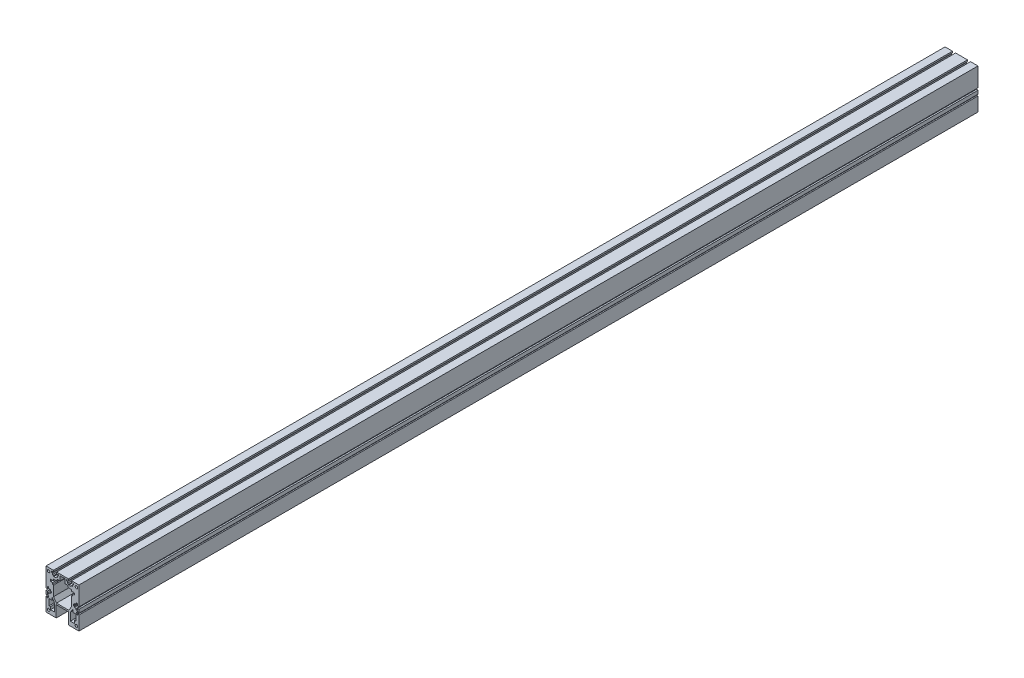
SolidWorks part; units mm, degrees
ref_plane "前视基准面" through (0, 0, 0) normal (0, 0, 1) x (1, 0, 0)
ref_plane "上视基准面" through (0, 0, 0) normal (0, 1, 0) x (1, 0, 0)
ref_plane "右视基准面" through (0, 0, 0) normal (1, 0, 0) x (0, 0, -1)
sketch "草图2" plane through (0, 0, 0) normal (0, 0, 1) x (1, 0, 0)
  line L0 (-18.1, 40) -> (-18.1, 37)
  line L1 (-33, 40) -> (-18.1, 40)
  line L2 (-33, 40) -> (-33, 2.0496)
  line L3 (-33, -40) -> (33, -40)
  line L4 (33, 40) -> (33, 2.0496)
  line L5 (-33, 40) -> (33, -40) construction
  line L6 (-33, -40) -> (33, 40) construction
  line L7 (-27.8, 33.5) -> (27.8, 33.5) construction
  line L8 (-27.8, 33.5) -> (-27.8, -33.5) construction
  line L9 (-27.8, -33.5) -> (27.8, -33.5) construction
  line L10 (27.8, 33.5) -> (27.8, -33.5) construction
  line L11 (-27.8, 33.5) -> (27.8, -33.5) construction
  line L12 (-27.8, -33.5) -> (27.8, 33.5) construction
  line L13 (-18.1, 37) -> (-22.1, 37)
  line L14 (-22.1, 37) -> (-22.1, 34.5)
  line L15 (-22.1, 34.5) -> (-20.1, 34.5)
  line L16 (-20.1, 34.5) -> (-20.1, 31)
  line L17 (-20.1, 31) -> (-17.5, 31)
  line L18 (-17.5, 31) -> (-17.5, 29.4)
  line L19 (-17.5, 29.4) -> (-12.5, 29.4)
  line L20 (-15, 29.4) -> (-15, 48.3161) construction
  line L21 (-12.5, 31) -> (-12.5, 29.4)
  line L22 (-9.9, 31) -> (-12.5, 31)
  line L23 (-9.9, 34.5) -> (-9.9, 31)
  line L24 (-7.9, 34.5) -> (-9.9, 34.5)
  line L25 (-7.9, 37) -> (-7.9, 34.5)
  line L26 (-11.9, 37) -> (-7.9, 37)
  line L27 (-11.9, 40) -> (-11.9, 37)
  line L28 (-11.9, 40) -> (11.9, 40)
  line L29 (0, 0) -> (0, 48.3161) construction
  line L30 (11.9, 40) -> (11.9, 37)
  line L31 (11.9, 37) -> (7.9, 37)
  line L32 (7.9, 37) -> (7.9, 34.5)
  line L33 (7.9, 34.5) -> (9.9, 34.5)
  line L34 (9.9, 34.5) -> (9.9, 31)
  line L35 (9.9, 31) -> (12.5, 31)
  line L36 (12.5, 31) -> (12.5, 29.4)
  line L37 (17.5, 29.4) -> (12.5, 29.4)
  line L38 (17.5, 31) -> (17.5, 29.4)
  line L39 (20.1, 31) -> (17.5, 31)
  line L40 (20.1, 34.5) -> (20.1, 31)
  line L41 (22.1, 34.5) -> (20.1, 34.5)
  line L42 (22.1, 37) -> (22.1, 34.5)
  line L43 (18.1, 37) -> (22.1, 37)
  line L44 (18.1, 40) -> (18.1, 37)
  line L45 (18.1, 40) -> (33, 40)
  line L46 (-24.0002, 21.7881) -> (-17.9322, 21.7881)
  line L47 (-17.9322, 21.7881) -> (-17.9322, 24.7125)
  line L48 (-17.9322, 24.7125) -> (-10.6389, 24.7125)
  line L49 (-10.6389, 24.7125) -> (-10.6389, 28.1692)
  line L50 (-10.6389, 28.1692) -> (-4.9, 28.1692)
  line L51 (-4.9, 28.1692) -> (-4.9, 37)
  line L52 (-4.9, 37) -> (4.9, 37)
  line L53 (-24.0002, 21.7881) -> (-24.0002, 17.5528)
  line L54 (-24.0002, 17.5528) -> (-20.1431, 17.5528)
  line L55 (-20.1431, 17.5528) -> (-20.1431, 14.1747)
  line L56 (-20.1431, 14.1747) -> (-17.9322, 14.1747)
  line L57 (-17.9322, 14.1747) -> (-17.9322, -5.7521)
  line L58 (-17.9322, -5.7521) -> (-12.0458, -14)
  line L59 (-12.0458, -14) -> (0, -14)
  line L60 (0, 0) -> (0, -54.8405) construction
  line L61 (4.9, 28.1692) -> (4.9, 37)
  line L62 (10.6389, 24.7125) -> (10.6389, 28.1692)
  line L63 (10.6389, 28.1692) -> (4.9, 28.1692)
  line L64 (17.9322, 24.7125) -> (10.6389, 24.7125)
  line L65 (17.9322, 21.7881) -> (17.9322, 24.7125)
  line L66 (24.0002, 21.7881) -> (17.9322, 21.7881)
  line L67 (24.0002, 21.7881) -> (24.0002, 17.5528)
  line L68 (27.8, -33.5) -> (-27.8, 33.5) construction
  line L69 (27.8, 33.5) -> (-27.8, -33.5) construction
  line L70 (12.0458, -14) -> (0, -14)
  line L71 (17.9322, -5.7521) -> (12.0458, -14)
  line L72 (17.9322, 14.1747) -> (17.9322, -5.7521)
  line L73 (20.1431, 14.1747) -> (17.9322, 14.1747)
  line L74 (20.1431, 17.5528) -> (20.1431, 14.1747)
  line L75 (24.0002, 17.5528) -> (20.1431, 17.5528)
  line L76 (-12.5, -40) -> (-12.5, -17)
  line L77 (-12.5, -17) -> (12.5, -17)
  line L78 (12.5, -17) -> (12.5, -40)
  line L79 (-33, -2.0496) -> (-30, -2.0496)
  line L80 (-30, -2.0496) -> (-30, -6.3482)
  line L81 (-27.8, -2.7555) -> (-26.6442, -2.7555)
  line L82 (-30, -6.3482) -> (-27.5, -6.3482)
  line L83 (-27.5, -6.3482) -> (-27.5, -3.5932)
  line L84 (-27.5, -3.5932) -> (-24, -3.5932)
  line L85 (-24, -3.5932) -> (-24, -1.3766)
  line L86 (-22.4, -1.3766) -> (-22.4, 1.3766)
  line L87 (-24, 1.3766) -> (-22.4, 1.3766)
  line L88 (-24, 3.5932) -> (-24, 1.3766)
  line L89 (-27.5, 3.5932) -> (-24, 3.5932)
  line L90 (-27.5, 6.3482) -> (-27.5, 3.5932)
  line L91 (-30, 6.3482) -> (-27.5, 6.3482)
  line L92 (-30, 2.0496) -> (-30, 6.3482)
  line L93 (-33, 2.0496) -> (-30, 2.0496)
  line L94 (24, -1.3766) -> (22.4, -1.3766)
  line L95 (33, 2.0496) -> (30, 2.0496)
  line L96 (30, 2.0496) -> (30, 6.3482)
  line L97 (30, 6.3482) -> (27.5, 6.3482)
  line L98 (27.5, 6.3482) -> (27.5, 3.5932)
  line L99 (27.5, 3.5932) -> (24, 3.5932)
  line L100 (24, 3.5932) -> (24, 1.3766)
  line L101 (24, 1.3766) -> (22.4, 1.3766)
  line L102 (22.4, -1.3766) -> (22.4, 1.3766)
  line L103 (24, -3.5932) -> (24, -1.3766)
  line L104 (27.5, -3.5932) -> (24, -3.5932)
  line L105 (27.5, -6.3482) -> (27.5, -3.5932)
  line L106 (30, -6.3482) -> (27.5, -6.3482)
  line L107 (27.8, -2.7555) -> (26.6442, -2.7555)
  line L108 (30, -2.0496) -> (30, -6.3482)
  line L109 (-20.9431, -8.11) -> (-15.8, -15.8603)
  line L110 (-15.8, -15.8603) -> (-15.8, -31.3609)
  line L111 (-15.8, -31.3609) -> (-24, -31.3609)
  line L112 (-24, -31.3609) -> (-24, -25.867)
  line L113 (-24, -25.867) -> (-26.6442, -25.867)
  line L114 (-26.6442, -25.867) -> (-26.6442, -13.4541)
  line L115 (-26.6442, -13.4541) -> (-20.9431, -13.4541)
  line L116 (-20.9431, -13.4541) -> (-20.9431, -8.11)
  line L117 (-33, -9.0684) -> (-30.7298, -9.0684)
  line L118 (-30.7298, -9.0684) -> (-30.7298, -7.473)
  line L119 (-30.7298, -7.473) -> (-29.1441, -7.473)
  line L120 (-29.1441, -7.473) -> (-29.1441, -9.0684)
  line L121 (-29.1441, -9.0684) -> (-27.8, -9.0684)
  line L122 (-27.8, -9.0684) -> (-27.8, -10.5684)
  line L123 (-36.4558, -10.5684) -> (-24.4752, -10.5684) construction
  line L124 (-27.8, -12.0684) -> (-27.8, -9.0684)
  line L125 (-29.1441, -12.0684) -> (-27.8, -12.0684)
  line L126 (-29.1441, -13.6637) -> (-29.1441, -12.0684)
  line L127 (-30.7298, -13.6637) -> (-29.1441, -13.6637)
  line L128 (-30.7298, -12.0684) -> (-30.7298, -13.6637)
  line L129 (-33, -12.0684) -> (-30.7298, -12.0684)
  line L130 (-33, -9.0684) -> (-30.7298, -9.0684)
  line L131 (-30.7298, -9.0684) -> (-30.7298, -7.473)
  line L132 (-30.7298, -7.473) -> (-29.1441, -7.473)
  line L133 (-29.1441, -7.473) -> (-29.1441, -9.0684)
  line L134 (-29.1441, -9.0684) -> (-27.8, -9.0684)
  line L135 (-27.8, -12.0684) -> (-27.8, -10.5684)
  line L136 (-29.1441, -12.0684) -> (-27.8, -12.0684)
  line L137 (-29.1441, -13.6637) -> (-29.1441, -12.0684)
  line L138 (-30.7298, -13.6637) -> (-29.1441, -13.6637)
  line L139 (-30.7298, -12.0684) -> (-30.7298, -13.6637)
  line L140 (-33, -12.0684) -> (-30.7298, -12.0684)
  line L141 (29.1441, -12.0684) -> (27.8, -12.0684)
  line L142 (29.1441, -13.6637) -> (29.1441, -12.0684)
  line L143 (24, -31.3609) -> (24, -25.867)
  line L144 (15.8, -31.3609) -> (24, -31.3609)
  line L145 (15.8, -15.8603) -> (15.8, -31.3609)
  line L146 (20.9431, -13.4541) -> (20.9431, -8.11)
  line L147 (26.6442, -13.4541) -> (20.9431, -13.4541)
  line L148 (26.6442, -25.867) -> (26.6442, -13.4541)
  line L149 (24, -25.867) -> (26.6442, -25.867)
  line L150 (20.9431, -8.11) -> (15.8, -15.8603)
  line L151 (33, -12.0684) -> (30.7298, -12.0684)
  line L152 (30.7298, -12.0684) -> (30.7298, -13.6637)
  line L153 (30.7298, -13.6637) -> (29.1441, -13.6637)
  line L154 (29.1441, -9.0684) -> (27.8, -9.0684)
  line L155 (29.1441, -7.473) -> (29.1441, -9.0684)
  line L156 (30.7298, -7.473) -> (29.1441, -7.473)
  line L157 (30.7298, -9.0684) -> (30.7298, -7.473)
  line L158 (33, -9.0684) -> (30.7298, -9.0684)
  line L159 (33, -12.0684) -> (30.7298, -12.0684)
  line L160 (30.7298, -12.0684) -> (30.7298, -13.6637)
  line L161 (30.7298, -13.6637) -> (29.1441, -13.6637)
  line L162 (27.8, -12.0684) -> (27.8, -9.0684)
  line L163 (27.8, -9.0684) -> (27.8, -10.5684)
  line L164 (29.1441, -9.0684) -> (27.8, -9.0684)
  line L165 (29.1441, -7.473) -> (29.1441, -9.0684)
  line L166 (30.7298, -7.473) -> (29.1441, -7.473)
  line L167 (30.7298, -9.0684) -> (30.7298, -7.473)
  line L168 (33, -9.0684) -> (30.7298, -9.0684)
  line L169 (33, -2.0496) -> (30, -2.0496)
  line L170 (33, 1.2445) -> (33, -9.0684)
  line L171 (33, -12.0684) -> (33, -40)
  line L172 (-22.4, 0) -> (-43.3501, 0) construction
  line L173 (-24, -1.3766) -> (-22.4, -1.3766)
  line L174 (-33, -2.0496) -> (-33, -40)
  circle A0 centre (-27.8, 33.5) radius 2.5
  circle A1 centre (27.8, 33.5) radius 2.5
  circle A2 centre (27.8, -33.5) radius 2.5
  circle A3 centre (-27.8, -33.5) radius 2.5
  point P0 (0, 0)
  point P7 (0, 0)
  point P32 (-18.1, 38.5)
  point P69 (0, 37)
  point P85 (0, -17)
  point P137 (-27.8, -9.8184)
  point P138 (-27.8, -11.3184)
  point P145 (-27.8, -9.8184)
  dimension "D5" = 5
  dimension "D6" = 5
  dimension "D7" = 5
  dimension "D8" = 5
  dimension "D1" = 66
  dimension "D2" = 80
  dimension "D3" = 55.6
  dimension "D4" = 67
  dimension "D9" = 14.2
  dimension "D10" = 6.2
  dimension "D11" = 10.2
  dimension "D12" = 18
  dimension "D13" = 3
  dimension "D14" = 2.5
  dimension "D15" = 10.6
  dimension "D16" = 9
  dimension "D17" = 5
  dimension "D18" = 25
  dimension "D19" = 0
  dimension "D20" = 23
  dimension "D21" = 3
  dimension "D22" = 3
  dimension "D23" = 3
  dimension "D28" = 3.3
  dimension "D29" = 3
  dimension "D30" = 3
  dimension "D31" = 0
  dimension "D32" = 3.5
extrude "凸台-拉伸1" add sketch "草图2" along normal blind 1800
ref_plane "基准面1" through (-15, 0, 0) normal (1, 0, 0) x (0, 0, -1)
ref_plane "基准面2" through (0, 0, 900) normal (0, 0, -1) x (-1, 0, 0)
